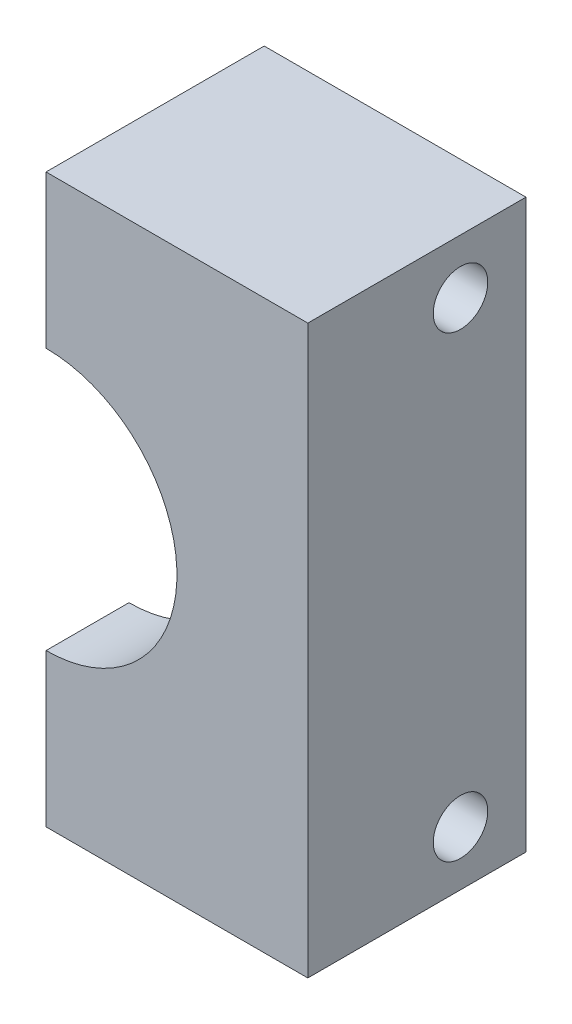
SolidWorks part; units mm, degrees
ref_plane "Plan de face" through (0, 0, 0) normal (0, 0, 1) x (1, 0, 0)
ref_plane "Plan de dessus" through (0, 0, 0) normal (0, 1, 0) x (1, 0, 0)
ref_plane "Plan de droite" through (0, 0, 0) normal (1, 0, 0) x (0, 0, -1)
sketch "Esquisse1" plane through (0, 0, 0) normal (0, 0, 1) x (1, 0, 0)
  line L1 (0, 0) -> (-12, 0)
  line L2 (0, 0) -> (0, 26)
  line L3 (0, 26) -> (-12, 26)
  line L4 (-12, 0) -> (-12, 26)
  circle A0 centre (-12, 13) radius 8
  dimension "D1" = 16
  dimension "D3" = 12
  dimension "D2" = 26
extrude "Boss.-Extru.1" add sketch "Esquisse1" along normal blind 10 contours A0 L4 L1 L2 L3
sketch "Esquisse2" plane through (0, 0, 10) normal (0, 0, 1) x (1, 0, 0)
  line L0 (-12, 23.2819) -> (-12, 2.7181)
  circle A0 centre (-12, 13) radius 10.2819
  circle A1 centre (-12, 13) radius 6
  arc M1 (-12, 21) -> (-12, 5) centre (-12, 13) cw
  dimension "D1" = 12
extrude "Boss.-Extru.2" add sketch "Esquisse2" against normal blind 3.8 contours A1 L0 M1
sketch "Esquisse3" plane through (-12, 0, 0) normal (-1, 0, 0) x (0, 0, 1)
  line L0 (0, 21) -> (0, 26) construction
  line L1 (0, 0) -> (0, 5) construction
  line L2 (10, 0) -> (0, 0) construction
  line L3 (10, 26) -> (0, 26) construction
  circle A0 centre (3, 23.5) radius 1.25
  circle A1 centre (3, 2.5) radius 1.25
  dimension "D1" = 2.5
  dimension "D2" = 2.5
  dimension "D3" = 3
  dimension "D4" = 3
  dimension "D5" = 2.5
  dimension "D6" = 2.5
extrude "Enlèv. mat.-Extru.1" cut sketch "Esquisse3" against normal through all
